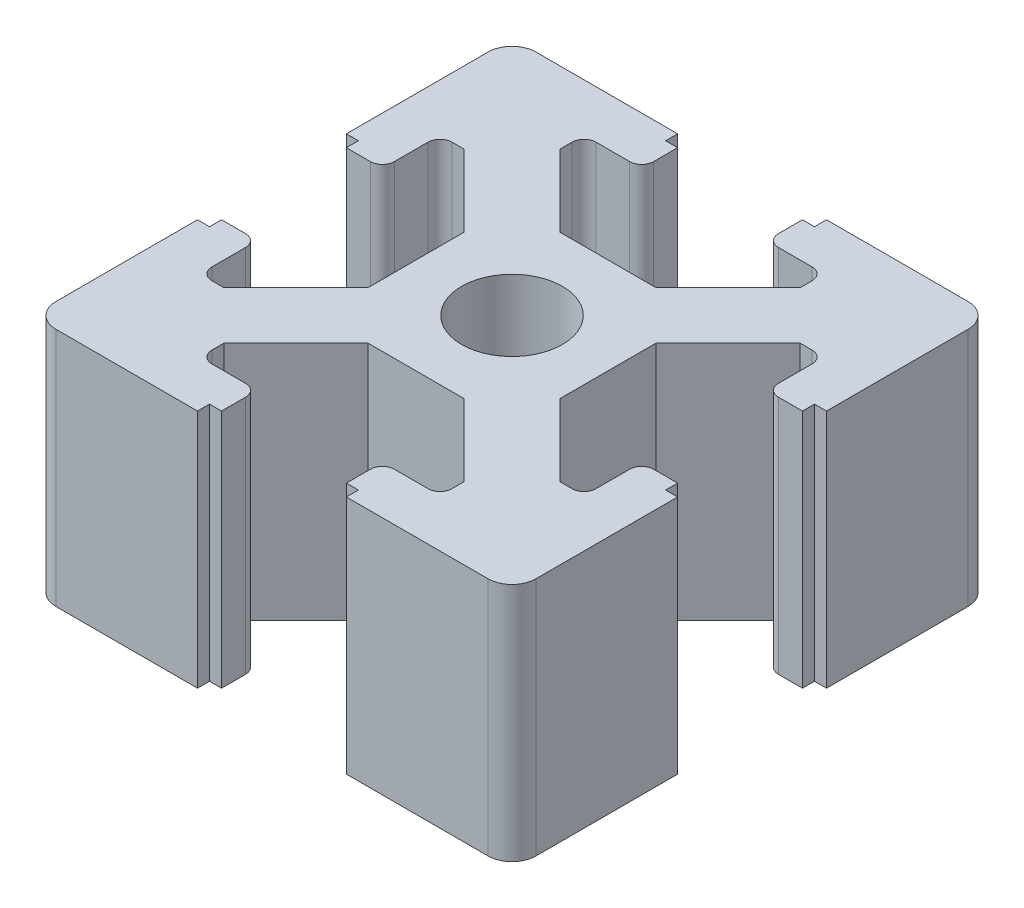
SolidWorks part; units mm, degrees
ref_plane "정면" through (0, 0, 0) normal (0, 0, 1) x (1, 0, 0)
ref_plane "윗면" through (0, 0, 0) normal (0, 1, 0) x (1, 0, 0)
ref_plane "우측면" through (0, 0, 0) normal (1, 0, 0) x (0, 0, -1)
sketch "스케치1" plane through (0, 0, 0) normal (0, 1, 0) x (1, 0, 0)
  line L0 (0, 4) -> (0, -4) construction
  line L1 (2, -4) -> (-2, -4)
  line L2 (-2, -4) -> (-5, -7)
  line L3 (-5, -7) -> (-5, -8) construction
  line L4 (-5, -8) -> (-2.6, -8) construction
  line L5 (-2.6, -8) -> (-2.6, -9.5) construction
  line L6 (-2.6, -9.5) -> (-3.1, -9.5)
  line L7 (-3.1, -9.5) -> (-3.1, -10)
  line L8 (-3.1, -10) -> (-9, -10)
  line L9 (-9, -10) -> (-9, -9) construction
  line L10 (-9, -10) -> (-10, -10) construction
  line L11 (-9, -9) -> (-10, -9) construction
  line L12 (-10, -10) -> (-10, -9) construction
  line L13 (3.1, -8) -> (3.1, -8.5) construction
  line L14 (2.6, -8.5) -> (3.1, -8.5) construction
  line L15 (2.6, -8) -> (2.6, -8.5) construction
  line L16 (-5, -7) -> (-5, -7.5)
  line L17 (-5, -8) -> (-4.5, -8) construction
  line L18 (-5, -8) -> (-5, -7.5) construction
  line L19 (-5, -7.5) -> (-4.5, -7.5) construction
  line L20 (-4.5, -8) -> (-4.5, -7.5) construction
  line L21 (-2.6, -9.5) -> (-2.6, -8.5)
  line L22 (-2.6, -8) -> (-3.1, -8) construction
  line L23 (-2.6, -8) -> (-2.6, -8.5) construction
  line L24 (-2.6, -8.5) -> (-3.1, -8.5) construction
  line L25 (-3.1, -8) -> (-3.1, -8.5) construction
  line L26 (-4.5, -8) -> (-3.1, -8)
  line L27 (2.6, -8) -> (3.1, -8) construction
  line L28 (4.5, -8) -> (4.5, -7.5) construction
  line L29 (5, -7.5) -> (4.5, -7.5) construction
  line L30 (5, -8) -> (5, -7.5) construction
  line L31 (5, -8) -> (4.5, -8) construction
  line L32 (10, -10) -> (10, -9) construction
  line L33 (9, -9) -> (10, -9) construction
  line L34 (9, -10) -> (10, -10) construction
  line L35 (9, -10) -> (9, -9) construction
  line L36 (2.6, -8) -> (2.6, -9.5) construction
  line L37 (5, -8) -> (2.6, -8) construction
  line L38 (5, -7) -> (5, -8) construction
  line L39 (4.5, -8) -> (3.1, -8)
  line L40 (2.6, -9.5) -> (2.6, -8.5)
  line L41 (5, -7) -> (5, -7.5)
  line L42 (3.1, -10) -> (9, -10)
  line L43 (3.1, -9.5) -> (3.1, -10)
  line L44 (2.6, -9.5) -> (3.1, -9.5)
  line L45 (2, -4) -> (5, -7)
  line L46 (-4, -2) -> (-4, 2)
  line L47 (-4, 2) -> (-7, 5)
  line L48 (-9.5, 2.6) -> (-9.5, 3.1)
  line L49 (-9.5, 3.1) -> (-10, 3.1)
  line L50 (-10, 3.1) -> (-10, 9)
  line L51 (-7, 5) -> (-7.5, 5)
  line L52 (-9.5, 2.6) -> (-8.5, 2.6)
  line L53 (-8, 4.5) -> (-8, 3.1)
  line L54 (-8, -4.5) -> (-8, -3.1)
  line L55 (-9.5, -2.6) -> (-8.5, -2.6)
  line L56 (-7, -5) -> (-7.5, -5)
  line L57 (-10, -3.1) -> (-10, -9)
  line L58 (-9.5, -3.1) -> (-10, -3.1)
  line L59 (-9.5, -2.6) -> (-9.5, -3.1)
  line L60 (-4, -2) -> (-7, -5)
  line L61 (4, 0) -> (-4, 0) construction
  line L62 (-7, 5) -> (-8, 5) construction
  line L63 (-8, 5) -> (-8, 2.6) construction
  line L64 (-8, 2.6) -> (-9.5, 2.6) construction
  line L65 (-10, 9) -> (-9, 9) construction
  line L66 (-10, 9) -> (-10, 10) construction
  line L67 (-9, 9) -> (-9, 10) construction
  line L68 (-10, 10) -> (-9, 10) construction
  line L69 (-8, -3.1) -> (-8.5, -3.1) construction
  line L70 (-8.5, -2.6) -> (-8.5, -3.1) construction
  line L71 (-8, -2.6) -> (-8.5, -2.6) construction
  line L72 (-8, 5) -> (-8, 4.5) construction
  line L73 (-8, 5) -> (-7.5, 5) construction
  line L74 (-7.5, 5) -> (-7.5, 4.5) construction
  line L75 (-8, 4.5) -> (-7.5, 4.5) construction
  line L76 (-8, 2.6) -> (-8, 3.1) construction
  line L77 (-8, 2.6) -> (-8.5, 2.6) construction
  line L78 (-8.5, 2.6) -> (-8.5, 3.1) construction
  line L79 (-8, 3.1) -> (-8.5, 3.1) construction
  line L80 (-8, -2.6) -> (-8, -3.1) construction
  line L81 (-8, -4.5) -> (-7.5, -4.5) construction
  line L82 (-7.5, -5) -> (-7.5, -4.5) construction
  line L83 (-8, -5) -> (-7.5, -5) construction
  line L84 (-8, -5) -> (-8, -4.5) construction
  line L85 (-10, -10) -> (-9, -10) construction
  line L86 (-9, -9) -> (-9, -10) construction
  line L87 (-10, -9) -> (-10, -10) construction
  line L88 (-10, -9) -> (-9, -9) construction
  line L89 (-8, -2.6) -> (-9.5, -2.6) construction
  line L90 (-8, -5) -> (-8, -2.6) construction
  line L91 (-7, -5) -> (-8, -5) construction
  line L92 (-2, 4) -> (2, 4)
  line L93 (2, 4) -> (5, 7)
  line L94 (2.6, 9.5) -> (3.1, 9.5)
  line L95 (3.1, 9.5) -> (3.1, 10)
  line L96 (3.1, 10) -> (9, 10)
  line L97 (5, 7) -> (5, 7.5)
  line L98 (2.6, 9.5) -> (2.6, 8.5)
  line L99 (4.5, 8) -> (3.1, 8)
  line L100 (-4.5, 8) -> (-3.1, 8)
  line L101 (-2.6, 9.5) -> (-2.6, 8.5)
  line L102 (-5, 7) -> (-5, 7.5)
  line L103 (-3.1, 10) -> (-9, 10)
  line L104 (-3.1, 9.5) -> (-3.1, 10)
  line L105 (-2.6, 9.5) -> (-3.1, 9.5)
  line L106 (-2, 4) -> (-5, 7)
  line L107 (0, -4) -> (0, 4) construction
  line L108 (5, 7) -> (5, 8) construction
  line L109 (5, 8) -> (2.6, 8) construction
  line L110 (2.6, 8) -> (2.6, 9.5) construction
  line L111 (9, 10) -> (9, 9) construction
  line L112 (9, 10) -> (10, 10) construction
  line L113 (9, 9) -> (10, 9) construction
  line L114 (10, 10) -> (10, 9) construction
  line L115 (-3.1, 8) -> (-3.1, 8.5) construction
  line L116 (-2.6, 8.5) -> (-3.1, 8.5) construction
  line L117 (-2.6, 8) -> (-2.6, 8.5) construction
  line L118 (5, 8) -> (4.5, 8) construction
  line L119 (5, 8) -> (5, 7.5) construction
  line L120 (5, 7.5) -> (4.5, 7.5) construction
  line L121 (4.5, 8) -> (4.5, 7.5) construction
  line L122 (2.6, 8) -> (3.1, 8) construction
  line L123 (2.6, 8) -> (2.6, 8.5) construction
  line L124 (2.6, 8.5) -> (3.1, 8.5) construction
  line L125 (3.1, 8) -> (3.1, 8.5) construction
  line L126 (-2.6, 8) -> (-3.1, 8) construction
  line L127 (-4.5, 8) -> (-4.5, 7.5) construction
  line L128 (-5, 7.5) -> (-4.5, 7.5) construction
  line L129 (-5, 8) -> (-5, 7.5) construction
  line L130 (-5, 8) -> (-4.5, 8) construction
  line L131 (-10, 10) -> (-10, 9) construction
  line L132 (-9, 9) -> (-10, 9) construction
  line L133 (-9, 10) -> (-10, 10) construction
  line L134 (-9, 10) -> (-9, 9) construction
  line L135 (-2.6, 8) -> (-2.6, 9.5) construction
  line L136 (-5, 8) -> (-2.6, 8) construction
  line L137 (-5, 7) -> (-5, 8) construction
  line L138 (4, 2) -> (4, -2)
  line L139 (4, -2) -> (7, -5)
  line L140 (9.5, -2.6) -> (9.5, -3.1)
  line L141 (9.5, -3.1) -> (10, -3.1)
  line L142 (10, -3.1) -> (10, -9)
  line L143 (7, -5) -> (7.5, -5)
  line L144 (9.5, -2.6) -> (8.5, -2.6)
  line L145 (8, -4.5) -> (8, -3.1)
  line L146 (8, 4.5) -> (8, 3.1)
  line L147 (9.5, 2.6) -> (8.5, 2.6)
  line L148 (7, 5) -> (7.5, 5)
  line L149 (10, 3.1) -> (10, 9)
  line L150 (9.5, 3.1) -> (10, 3.1)
  line L151 (9.5, 2.6) -> (9.5, 3.1)
  line L152 (4, 2) -> (7, 5)
  line L153 (-4, 0) -> (4, 0) construction
  line L154 (7, -5) -> (8, -5) construction
  line L155 (8, -5) -> (8, -2.6) construction
  line L156 (8, -2.6) -> (9.5, -2.6) construction
  line L157 (10, -9) -> (9, -9) construction
  line L158 (10, -9) -> (10, -10) construction
  line L159 (9, -9) -> (9, -10) construction
  line L160 (10, -10) -> (9, -10) construction
  line L161 (8, 3.1) -> (8.5, 3.1) construction
  line L162 (8.5, 2.6) -> (8.5, 3.1) construction
  line L163 (8, 2.6) -> (8.5, 2.6) construction
  line L164 (8, -5) -> (8, -4.5) construction
  line L165 (8, -5) -> (7.5, -5) construction
  line L166 (7.5, -5) -> (7.5, -4.5) construction
  line L167 (8, -4.5) -> (7.5, -4.5) construction
  line L168 (8, -2.6) -> (8, -3.1) construction
  line L169 (8, -2.6) -> (8.5, -2.6) construction
  line L170 (8.5, -2.6) -> (8.5, -3.1) construction
  line L171 (8, -3.1) -> (8.5, -3.1) construction
  line L172 (8, 2.6) -> (8, 3.1) construction
  line L173 (8, 4.5) -> (7.5, 4.5) construction
  line L174 (7.5, 5) -> (7.5, 4.5) construction
  line L175 (8, 5) -> (7.5, 5) construction
  line L176 (8, 5) -> (8, 4.5) construction
  line L177 (10, 10) -> (9, 10) construction
  line L178 (9, 9) -> (9, 10) construction
  line L179 (10, 9) -> (10, 10) construction
  line L180 (10, 9) -> (9, 9) construction
  line L181 (8, 2.6) -> (9.5, 2.6) construction
  line L182 (8, 5) -> (8, 2.6) construction
  line L183 (7, 5) -> (8, 5) construction
  circle A0 centre (0, 0) radius 2.1
  arc A1 (-5, -7.5) -> (-4.5, -8) centre (-4.5, -7.5) ccw
  arc A2 (-3.1, -8) -> (-2.6, -8.5) centre (-3.1, -8.5) cw
  arc A3 (-9, -10) -> (-9.7071, -9.7071) centre (-9, -9) cw
  arc A4 (9, -10) -> (9.7071, -9.7071) centre (9, -9) ccw
  arc A5 (3.1, -8) -> (2.6, -8.5) centre (3.1, -8.5) ccw
  arc A6 (5, -7.5) -> (4.5, -8) centre (4.5, -7.5) cw
  arc A7 (-7.5, 5) -> (-8, 4.5) centre (-7.5, 4.5) ccw
  arc A8 (-8, 3.1) -> (-8.5, 2.6) centre (-8.5, 3.1) cw
  arc A9 (-10, 9) -> (-9.7071, 9.7071) centre (-9, 9) cw
  arc A10 (-10, -9) -> (-9.7071, -9.7071) centre (-9, -9) ccw
  arc A11 (-8, -3.1) -> (-8.5, -2.6) centre (-8.5, -3.1) ccw
  arc A12 (-7.5, -5) -> (-8, -4.5) centre (-7.5, -4.5) cw
  arc A13 (5, 7.5) -> (4.5, 8) centre (4.5, 7.5) ccw
  arc A14 (3.1, 8) -> (2.6, 8.5) centre (3.1, 8.5) cw
  arc A15 (9, 10) -> (9.7071, 9.7071) centre (9, 9) cw
  arc A16 (-9, 10) -> (-9.7071, 9.7071) centre (-9, 9) ccw
  arc A17 (-3.1, 8) -> (-2.6, 8.5) centre (-3.1, 8.5) ccw
  arc A18 (-5, 7.5) -> (-4.5, 8) centre (-4.5, 7.5) cw
  arc A19 (7.5, -5) -> (8, -4.5) centre (7.5, -4.5) ccw
  arc A20 (8, -3.1) -> (8.5, -2.6) centre (8.5, -3.1) cw
  arc A21 (10, -9) -> (9.7071, -9.7071) centre (9, -9) cw
  arc A22 (10, 9) -> (9.7071, 9.7071) centre (9, 9) ccw
  arc A23 (8, 3.1) -> (8.5, 2.6) centre (8.5, 3.1) ccw
  arc A24 (7.5, 5) -> (8, 4.5) centre (7.5, 4.5) cw
  point P6 (0, 0)
  point P9 (0, -4)
  point P52 (-4, 0)
  point P92 (0, 4)
  point P132 (4, 0)
  point P167 (0, 0)
  dimension "D1" = 4.2
  dimension "D9" = 1
  dimension "D2" = 4
  dimension "D3" = 4
  dimension "D4" = 3
  dimension "D5" = 1
  dimension "D6" = 2
  dimension "D7" = 2.6
  dimension "D8" = 3.1
  dimension "D10" = 1
  dimension "D11" = 0.5
  dimension "D12" = 0.5
  dimension "D13" = 0.5
  dimension "D14" = 5
  dimension "D15" = 45
  dimension "D16" = 1
  dimension "D17" = 10
  dimension "D18" = 4
extrude "보스-돌출1" add sketch "스케치1" along normal blind 10
